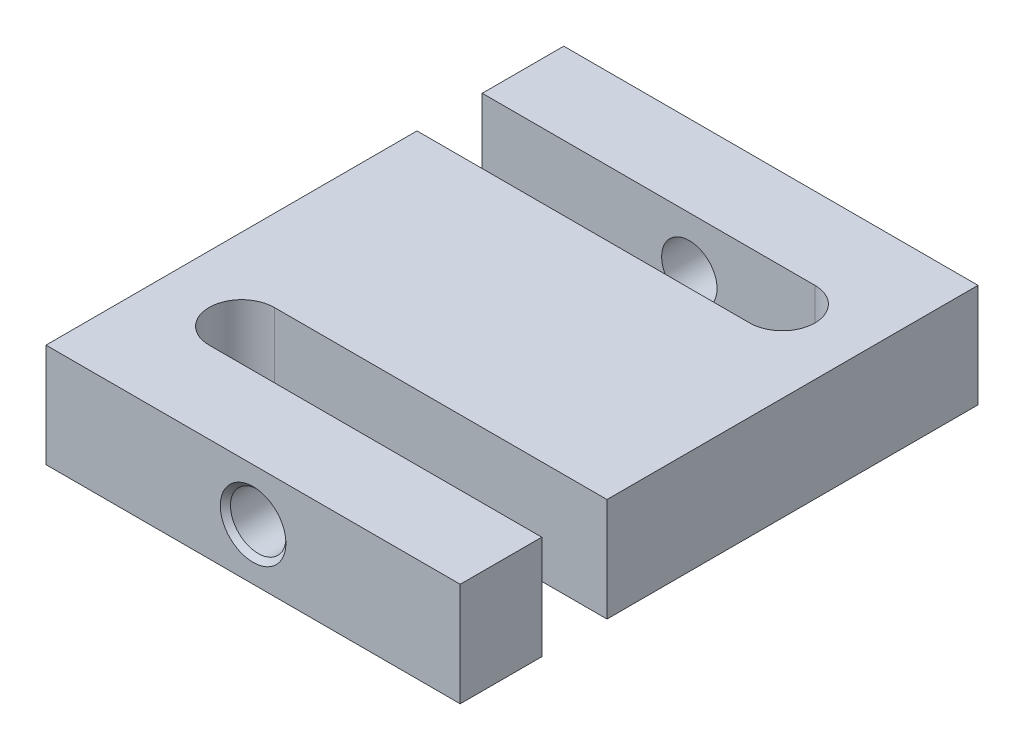
SolidWorks part; units mm, degrees
ref_plane "Front Plane" through (0, 0, 0) normal (0, 0, 1) x (1, 0, 0)
ref_plane "Top Plane" through (0, 0, 0) normal (0, 1, 0) x (1, 0, 0)
ref_plane "Right Plane" through (0, 0, 0) normal (1, 0, 0) x (0, 0, -1)
sketch "Sketch1" plane through (0, 0, 0) normal (0, 1, 0) x (1, 0, 0)
  line L1 (0, 0) -> (50.8, 0)
  line L2 (0, 0) -> (0, 63.5)
  line L3 (0, 63.5) -> (50.8, 63.5)
  line L4 (50.8, 0) -> (50.8, 63.5)
  dimension "D1" = 50.8
  dimension "D2" = 63.5
extrude "Boss-Extrude1" add sketch "Sketch1" along normal blind 12.7
hole_wizard "M8x1.25 Tapped Hole1" positions "Sketch2" profile "Sketch3" tap size "M8x1.25" standard "ANSI Metric"
sketch "Sketch2" plane through (0, 0, -63.5) normal (0, 0, -1) x (-1, 0, 0)
  line L1 (-50.8, 12.7) -> (0, 12.7) construction
  line L3 (-50.8, 12.7) -> (-50.8, 0) construction
  point P0 (-25.4, 6.35)
  dimension "D1" = 6.35
  dimension "D2" = 25.4
cosmetic thread "Hole Thread1" parameters "D1"=18.75, "D2"=8
sketch "Sketch3" plane through (25.4, 6.35, -63.5) normal (1, 0, 0) x (0, 1, 0)
  line L0 (0, 0) -> (0, 17.0429)
  line L1 (0, 17.0429) -> (3.4, 15)
  line L2 (3.4, 15) -> (3.4, 0.625)
  line L3 (3.4, 0.625) -> (4.025, 0)
  line L5 (4.025, 0) -> (0, 0)
  line L6 (-3.4, 0.625) -> (-4.025, 0) construction
  line L10 (0, 17.0429) -> (-3.4, 15) construction
  line L11 (0, -6.35) -> (0, 107.95) construction
  dimension "Tap Drill Dia." = 6.8
  dimension "Tap Drill Depth" = 15
  dimension "Near C'Sink Dia." = 8.05
  dimension "Near C'Sink Angle" = 90
  dimension "Drill Angle" = 118
hole_wizard "M8x1.25 Tapped Hole2" positions "Sketch7" profile "Sketch8" tap size "M8x1.25" standard "ANSI Metric"
sketch "Sketch7" plane through (0, 0, 0) normal (0, 0, 1) x (1, 0, 0)
  line L0 (0, 12.7) -> (0, 0) construction
  line L1 (0, 12.7) -> (50.8, 12.7) construction
  point P0 (25.4, 6.35)
  dimension "D1" = 25.4
  dimension "D2" = 6.35
sketch "Sketch8" plane through (25.4, 6.35, 0) normal (1, 0, 0) x (0, -1, 0)
  line L0 (0, 0) -> (0, 17.0429)
  line L1 (0, 17.0429) -> (3.4, 15)
  line L2 (3.4, 15) -> (3.4, 0.625)
  line L3 (3.4, 0.625) -> (4.025, 0)
  line L5 (4.025, 0) -> (0, 0)
  line L6 (-3.4, 0.625) -> (-4.025, 0) construction
  line L10 (0, 17.0429) -> (-3.4, 15) construction
  line L11 (0, -6.35) -> (0, 107.95) construction
  dimension "Tap Drill Dia." = 6.8
  dimension "Tap Drill Depth" = 15
  dimension "Near C'Sink Dia." = 8.05
  dimension "Near C'Sink Angle" = 90
  dimension "Drill Angle" = 118
cosmetic thread "Hole Thread2" parameters "D1"=18.75, "D2"=8
sketch "Sketch9" plane through (0, 12.7, 0) normal (0, 1, 0) x (1, 0, 0)
  line L0 (0, 63.5) -> (0, 0) construction
  line L1 (0, 53.5) -> (40.8, 53.5)
  line L2 (0, 53.5) -> (0, 45.5)
  line L3 (0, 45.5) -> (40.8, 45.5)
  line L5 (50.8, 63.5) -> (0, 63.5) construction
  line L6 (50.8, 0) -> (50.8, 63.5) construction
  line L7 (0, 0) -> (50.8, 0) construction
  line L8 (50.8, 18) -> (10, 18)
  line L9 (50.8, 18) -> (50.8, 10)
  line L10 (50.8, 10) -> (10, 10)
  arc A0 (40.8, 45.5) -> (40.8, 53.5) centre (40.8, 49.5) ccw
  arc A1 (10, 18) -> (10, 10) centre (10, 14) ccw
  dimension "D1" = 10
  dimension "D4" = 4
  dimension "D7" = 10
  dimension "D8" = 4
  dimension "D2" = 10
  dimension "D3" = 8
  dimension "D5" = 10
  dimension "D6" = 8
extrude "Cut-Extrude1" cut sketch "Sketch9" against normal through all
